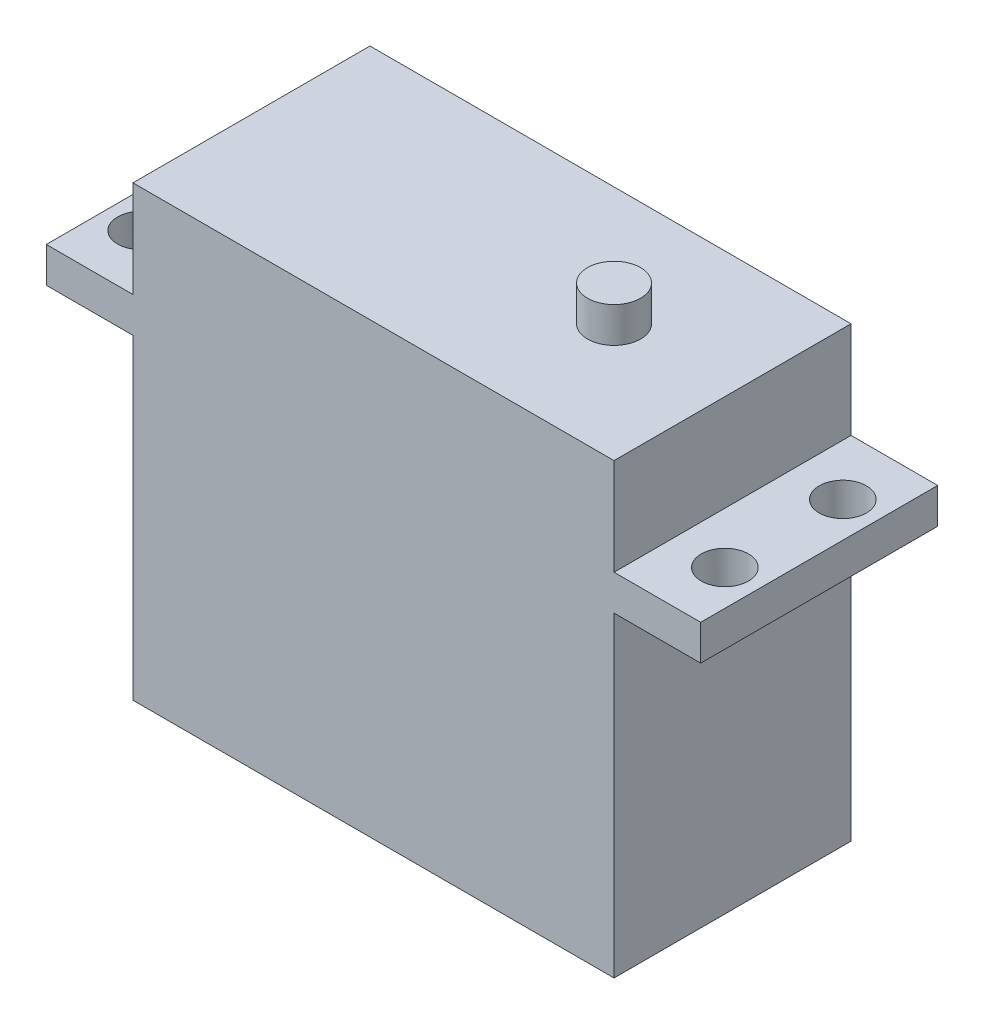
SolidWorks part; units mm, degrees
material "ABS"
ref_plane "Front Plane" through (0, 0, 0) normal (0, 0, 1) x (1, 0, 0)
ref_plane "Top Plane" through (0, 0, 0) normal (0, 1, 0) x (1, 0, 0)
ref_plane "Right Plane" through (0, 0, 0) normal (1, 0, 0) x (0, 0, -1)
sketch "Sketch1" plane through (0, 0, 0) normal (0, 0, 1) x (1, 0, 0)
  line L1 (0, 0) -> (40.8, 0)
  line L2 (0, 0) -> (0, 38)
  line L3 (0, 38) -> (40.8, 38)
  line L4 (40.8, 0) -> (40.8, 38)
  dimension "D1" = 40.8
  dimension "D2" = 38
extrude "Boss-Extrude1" add sketch "Sketch1" along normal blind 20.1
sketch "Sketch2" plane through (0, 0, 20.1) normal (0, 0, 1) x (1, 0, 0)
  line L0 (20.4, 26.8) -> (20.4, 0) construction
  line L1 (-7.35, 29.8) -> (48.15, 29.8)
  line L2 (-7.35, 29.8) -> (-7.35, 26.8)
  line L3 (-7.35, 26.8) -> (48.15, 26.8)
  line L4 (48.15, 29.8) -> (48.15, 26.8)
  line L5 (0, 0) -> (40.8, 0) construction
  dimension "D1" = 26.8
  dimension "D2" = 3
  dimension "D3" = 55.5
extrude "Boss-Extrude2" add sketch "Sketch2" against normal up to surface (20.1 mm away) up to face at (20.4, 19, 0)
sketch "Sketch3" plane through (0, 29.8, 0) normal (0, 1, 0) x (1, 0, 0)
  line L0 (-4.35, -10.05) -> (45.15, -10.05) construction
  line L1 (-4.35, -15.05) -> (45.15, -15.05) construction
  line L2 (-4.35, -15.05) -> (-4.35, -5.05) construction
  line L3 (-4.35, -5.05) -> (45.15, -5.05) construction
  line L4 (45.15, -15.05) -> (45.15, -5.05) construction
  line L6 (0, -20.1) -> (0, 0) construction
  line L7 (40.8, 0) -> (0, 0) construction
  circle A0 centre (-4.35, -5.05) radius 2
  circle A1 centre (-4.35, -15.05) radius 2
  circle A2 centre (45.15, -15.05) radius 2
  circle A3 centre (45.15, -5.05) radius 2
  point P14 (0, -10.05)
  point P15 (20.4, 0)
  point P16 (20.4, -10.05)
  dimension "D1" = 4
  dimension "D2" = 49.5
  dimension "D3" = 10
extrude "Cut-Extrude1" cut sketch "Sketch3" against normal through all
sketch "Sketch4" plane through (0, 38, 0) normal (0, 1, 0) x (1, 0, 0)
  line L0 (40.8, -20.1) -> (40.8, 0) construction
  line L1 (40.8, 0) -> (0, 0) construction
  line L2 (40.8, -20.1) -> (0, -20.1) construction
  circle A0 centre (30.75, -10.05) radius 10.05 construction
  circle A1 centre (30.75, -10.05) radius 2.25
  dimension "D1" = 4.5
extrude "Boss-Extrude3" add sketch "Sketch4" along normal blind 3
